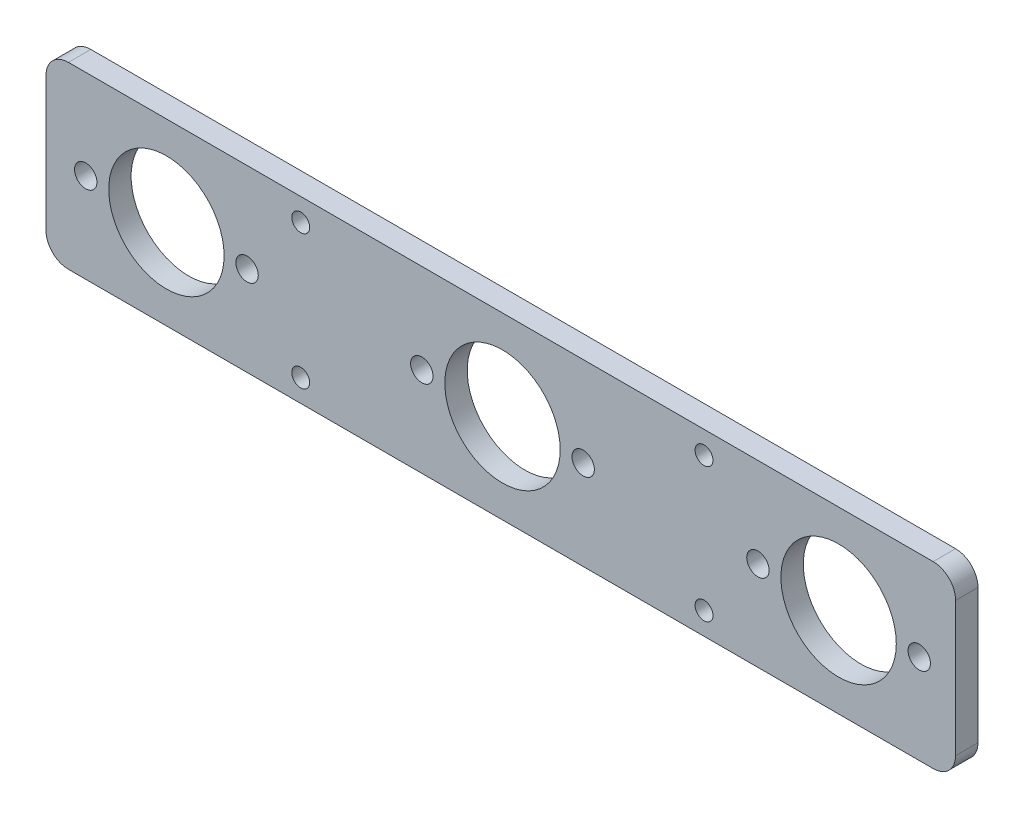
SolidWorks part; units mm, degrees
ref_plane "前基準面" through (0, 0, 0) normal (0, 0, 1) x (1, 0, 0)
ref_plane "上基準面" through (0, 0, 0) normal (0, 1, 0) x (1, 0, 0)
ref_plane "右基準面" through (0, 0, 0) normal (1, 0, 0) x (0, 0, -1)
sketch "草圖1" plane through (0, 0, 0) normal (0, 0, 1) x (1, 0, 0)
  line L5 (101.5869, -15.409) -> (101.5869, 14.591)
  line L6 (96.5869, 19.591) -> (-96.3939, 19.591)
  line L7 (-101.3939, 14.591) -> (-101.3939, -15.409)
  line L8 (96.5869, -20.409) -> (-96.3939, -20.409)
  circle A0 centre (-74.5237, -0.409) radius 12.875
  circle A1 centre (-56.5237, -0.409) radius 2.5
  circle A2 centre (-92.5237, -0.409) radius 2.5
  circle A3 centre (-17.5237, -0.409) radius 2.5
  circle A4 centre (0.4763, -0.409) radius 12.875
  circle A5 centre (18.4763, -0.409) radius 2.5
  circle A6 centre (57.4763, -0.409) radius 2.5
  circle A7 centre (75.4763, -0.409) radius 12.875
  circle A8 centre (93.4763, -0.409) radius 2.5
  arc A9 (96.5869, -20.409) -> (101.5869, -15.409) centre (96.5869, -15.409) ccw
  arc A10 (101.5869, 14.591) -> (96.5869, 19.591) centre (96.5869, 14.591) ccw
  arc A11 (-96.3939, -20.409) -> (-101.3939, -15.409) centre (-96.3939, -15.409) cw
  arc A12 (-101.3939, 14.591) -> (-96.3939, 19.591) centre (-96.3939, 14.591) cw
  circle A13 centre (-44.5558, 14.591) radius 2
  circle A14 centre (-44.5558, -15.409) radius 2
  circle A15 centre (45.4506, 14.591) radius 2
  circle A16 centre (45.4506, -15.409) radius 2
  dimension "D1" = 5
extrude "填料-伸長1" add sketch "草圖1" along normal blind 5
